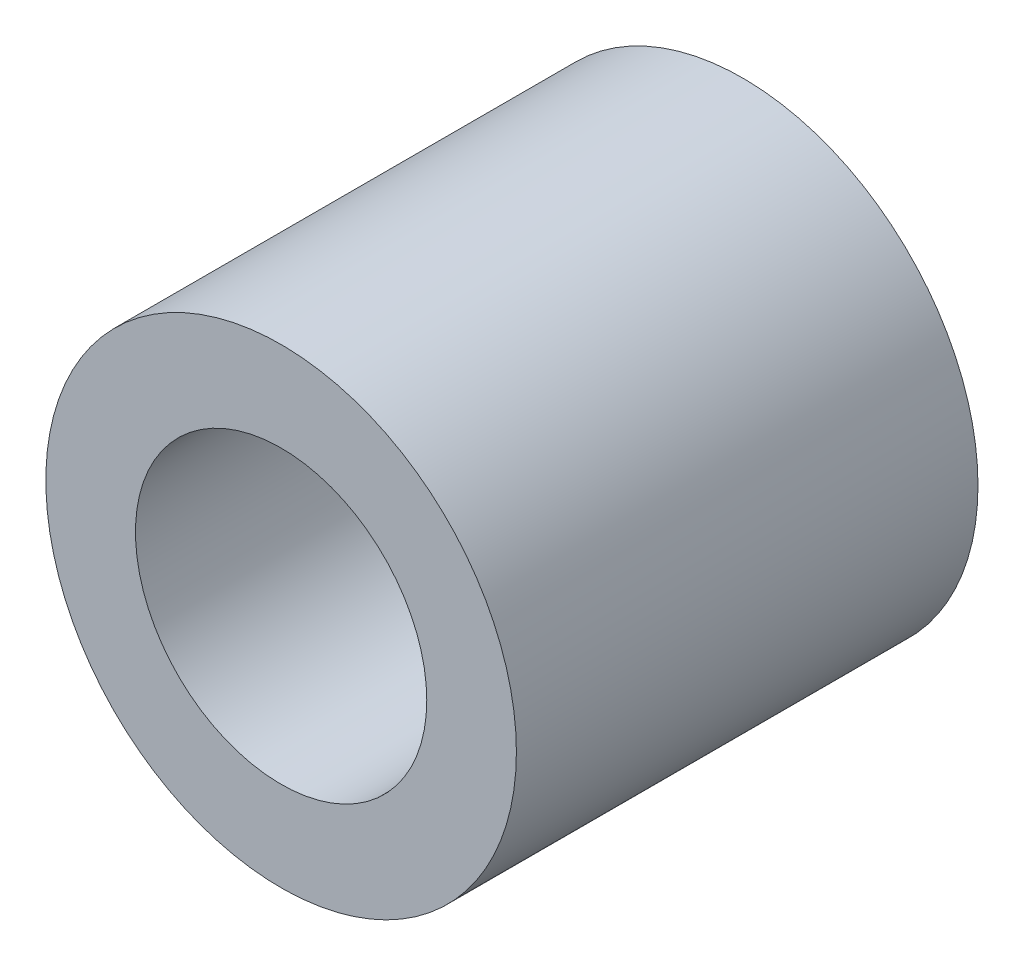
SolidWorks part; units mm, degrees
ref_plane "前视基准面" through (0, 0, 0) normal (0, 0, 1) x (1, 0, 0)
ref_plane "上视基准面" through (0, 0, 0) normal (0, 1, 0) x (1, 0, 0)
ref_plane "右视基准面" through (0, 0, 0) normal (1, 0, 0) x (0, 0, -1)
other "Configuration Table"
sketch "草图1" plane through (0, 0, 0) normal (0, 0, 1) x (1, 0, 0)
  circle A0 centre (0, 0) radius 3.25
  circle A1 centre (0, 0) radius 5.25
  dimension "D1" = 6.5
  dimension "2" = 2
extrude "凸台-拉伸1" add sketch "草图1" along normal blind 10.3
